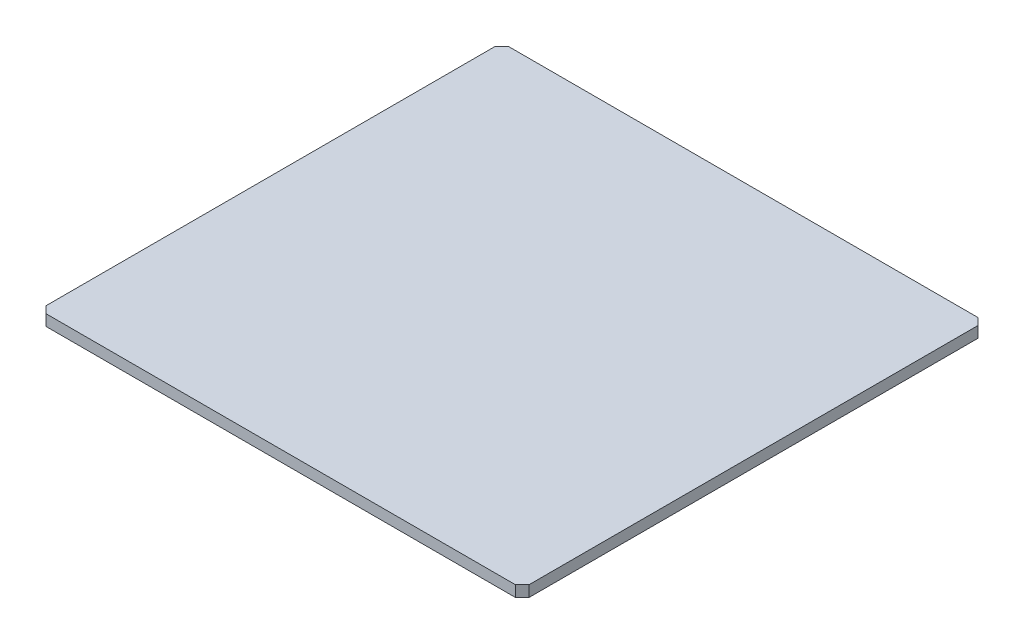
SolidWorks part; units mm, degrees
ref_plane "Front Plane" through (0, 0, 0) normal (0, 0, 1) x (1, 0, 0)
ref_plane "Top Plane" through (0, 0, 0) normal (0, 1, 0) x (1, 0, 0)
ref_plane "Right Plane" through (0, 0, 0) normal (1, 0, 0) x (0, 0, -1)
sketch "Sketch1" plane through (0, 0, 0) normal (0, 1, 0) x (1, 0, 0)
  line L0 (0.1017, 94.1375) -> (1.5263, 95.5621)
  line L1 (0.1017, -0.0104) -> (99.8983, -0.0104) construction
  line L2 (0.1017, -0.0104) -> (0.1017, 95.5621) construction
  line L3 (0.1017, 95.5621) -> (99.8983, 95.5621) construction
  line L4 (99.8983, -0.0104) -> (99.8983, 95.5621) construction
  line L5 (1.5263, 95.5621) -> (98.4737, 95.5621)
  line L6 (98.4737, 95.5621) -> (99.8983, 94.1375)
  line L7 (99.8983, 94.1375) -> (99.8983, 1.4142)
  line L8 (99.8983, 1.4142) -> (98.4737, -0.0104)
  line L9 (98.4737, -0.0104) -> (1.5263, -0.0104)
  line L10 (1.5263, -0.0104) -> (0.1017, 1.4142)
  line L11 (0.1017, 1.4142) -> (0.1017, 94.1375)
extrude "Boss-Extrude1" add sketch "Sketch1" along normal blind 2.286
ref_plane "center-of-slot" through (0, 1.143, 0) normal (0, 1, 0) x (1, 0, 0)
